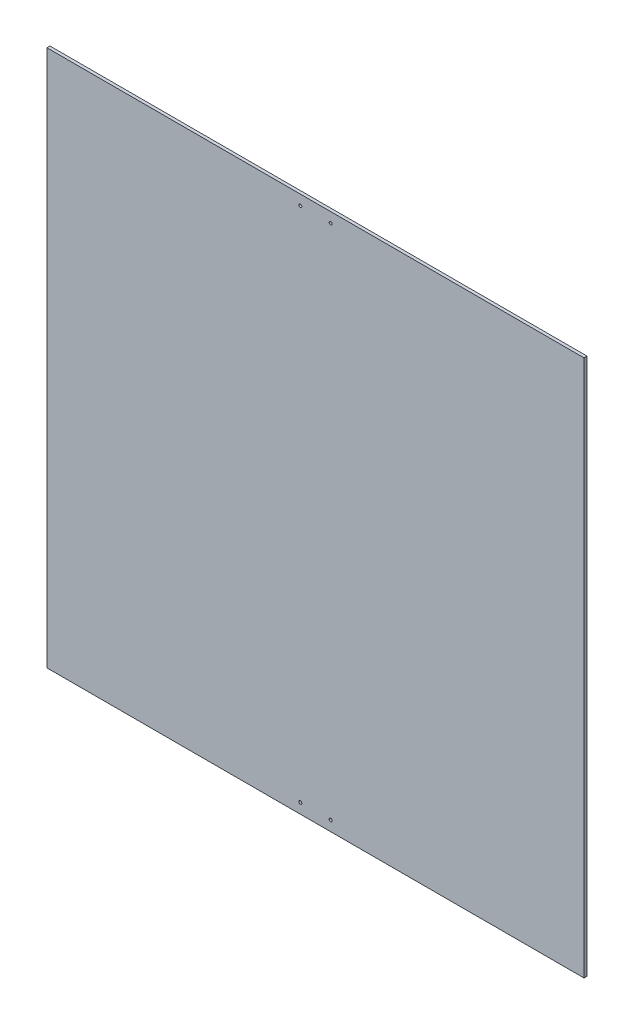
SolidWorks part; units mm, degrees
ref_plane "Plan de face" through (0, 0, 0) normal (0, 0, 1) x (1, 0, 0)
ref_plane "Plan de dessus" through (0, 0, 0) normal (0, 1, 0) x (1, 0, 0)
ref_plane "Plan de droite" through (0, 0, 0) normal (1, 0, 0) x (0, 0, -1)
sketch "Esquisse1" plane through (0, 0, 0) normal (0, 0, 1) x (1, 0, 0)
  line L1 (0, 0) -> (-530, 0)
  line L2 (0, 0) -> (0, 530)
  line L3 (0, 530) -> (-530, 530)
  line L4 (-530, 0) -> (-530, 530)
  dimension "D1" = 530
extrude "Boss.-Extru.1" add sketch "Esquisse1" along normal blind 3
sketch "Esquisse2" plane through (0, 0, 3) normal (0, 0, 1) x (1, 0, 0)
  line L0 (-265, 530) -> (-265, 0) construction
  line L1 (0, 530) -> (-530, 530) construction
  line L2 (-530, 0) -> (0, 0) construction
  line L3 (-530, 265) -> (0, 265) construction
  line L4 (-530, 530) -> (-530, 0) construction
  line L5 (0, 0) -> (0, 530) construction
  circle A0 centre (-250, 520) radius 1.5
  circle A1 centre (-280, 520) radius 1.5
  circle A2 centre (-250, 10) radius 1.5
  circle A3 centre (-280, 10) radius 1.5
  dimension "D1" = 3
  dimension "D2" = 15
  dimension "D3" = 10
extrude "Enlèv. mat.-Extru.1" cut sketch "Esquisse2" against normal blind 3
